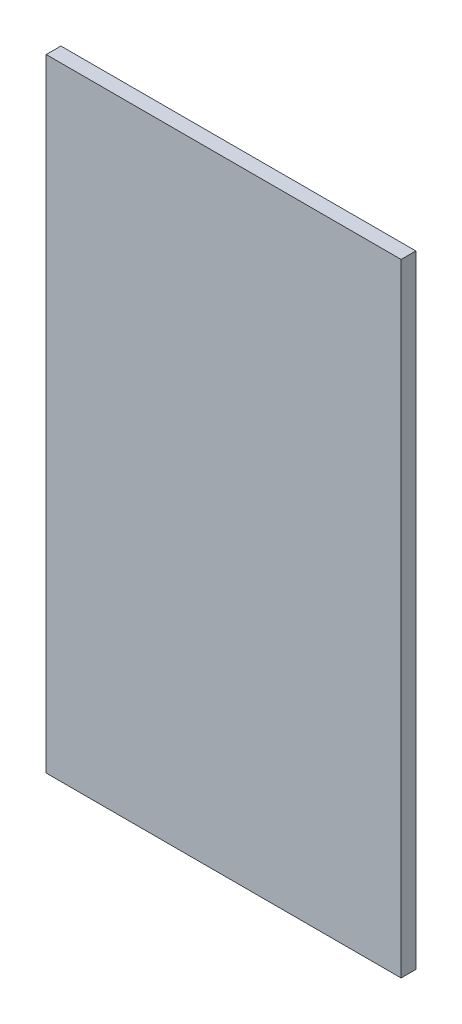
SolidWorks part; units mm, degrees
ref_plane "Front Plane" through (0, 0, 0) normal (0, 0, 1) x (1, 0, 0)
ref_plane "Top Plane" through (0, 0, 0) normal (0, 1, 0) x (1, 0, 0)
ref_plane "Right Plane" through (0, 0, 0) normal (1, 0, 0) x (0, 0, -1)
sketch "Sketch1" plane through (0, 0, 0) normal (0, 0, 1) x (1, 0, 0)
  line L1 (216.75, -380) -> (-216.75, -380)
  line L2 (216.75, -380) -> (216.75, 380)
  line L3 (216.75, 380) -> (-216.75, 380)
  line L4 (-216.75, -380) -> (-216.75, 380)
  line L5 (216.75, -380) -> (-216.75, 380) construction
  line L6 (216.75, 380) -> (-216.75, -380) construction
  point P0 (0, 0)
  dimension "D1" = 760
  dimension "D2" = 433.5
extrude "Boss-Extrude1" add sketch "Sketch1" along normal blind 18
equation "\"H_DSP\"=18"
equation "\"D1@Boss-Extrude1\"=\"H_DSP\""
